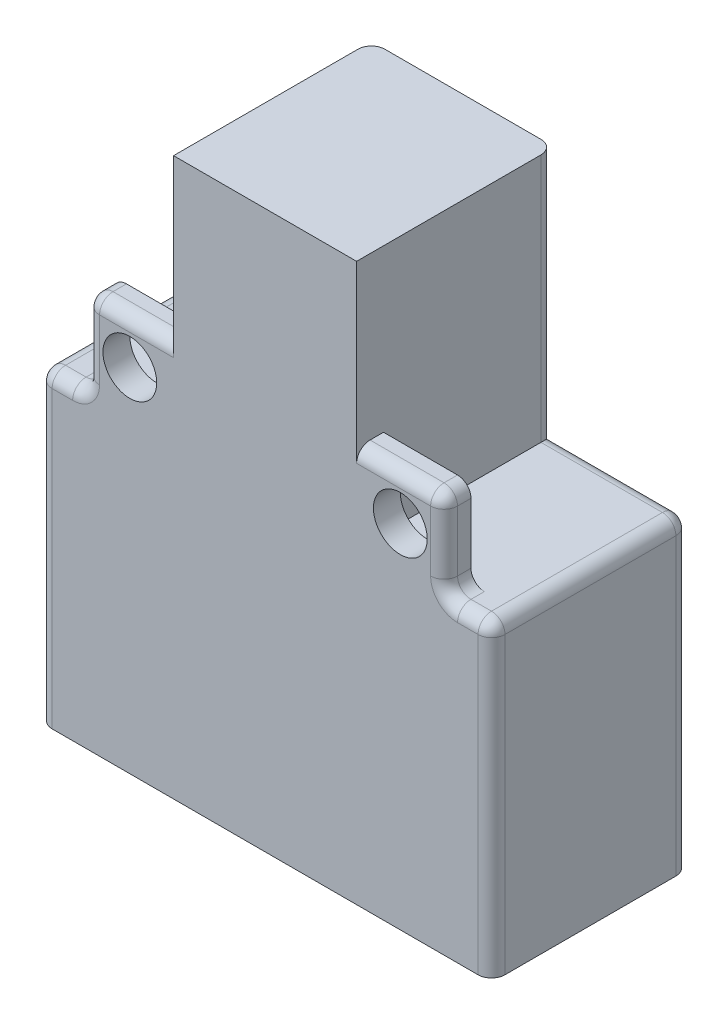
SolidWorks part; units mm, degrees
material "Custom Plastic"
ref_plane "Front Plane" through (0, 0, 0) normal (0, 0, 1) x (1, 0, 0)
ref_plane "Top Plane" through (0, 0, 0) normal (0, 1, 0) x (1, 0, 0)
ref_plane "Right Plane" through (0, 0, 0) normal (1, 0, 0) x (0, 0, -1)
sketch "Sketch1" plane through (0, 0, 0) normal (0, 1, 0) x (1, 0, 0)
  line L1 (-10.3392, 6.7346) -> (23.3108, 6.7346)
  line L2 (-10.3392, 6.7346) -> (-10.3392, -7.9654)
  line L3 (-10.3392, -7.9654) -> (23.3108, -7.9654)
  line L4 (23.3108, 6.7346) -> (23.3108, -7.9654)
  dimension "D1" = 14.7
  dimension "D2" = 33.65
extrude "Boss-Extrude1" add sketch "Sketch1" along normal blind 22.9
sketch "Sketch2" plane through (0, 22.9, 0) normal (0, 1, 0) x (1, 0, 0)
  line L0 (23.3108, 6.7346) -> (-10.3392, 6.7346) construction
  line L1 (-0.3142, 6.7346) -> (13.2858, 6.7346)
  line L2 (-0.3142, 6.7346) -> (-0.3142, -7.9654)
  line L3 (-0.3142, -7.9654) -> (13.2858, -7.9654)
  line L4 (13.2858, 6.7346) -> (13.2858, -7.9654)
  line L5 (-10.3392, -7.9654) -> (23.3108, -7.9654) construction
  line L6 (23.3108, -7.9654) -> (23.3108, 6.7346) construction
  dimension "D1" = 10.025
  dimension "D2" = 10.025
extrude "Boss-Extrude2" add sketch "Sketch2" along normal blind 18.5
sketch "Sketch3" plane through (0, 22.9, 0) normal (0, 1, 0) x (1, 0, 0)
  line L0 (-0.3142, 6.7346) -> (-0.3142, -7.9654) construction
  line L1 (-0.3142, -5.9654) -> (-6.8142, -5.9654)
  line L2 (-0.3142, -5.9654) -> (-0.3142, -7.9654)
  line L3 (-0.3142, -7.9654) -> (-6.8142, -7.9654)
  line L4 (-6.8142, -5.9654) -> (-6.8142, -7.9654)
  line L5 (-10.3392, -7.9654) -> (-0.3142, -7.9654) construction
  dimension "D1" = 6.5
  dimension "D2" = 2
extrude "Boss-Extrude3" add sketch "Sketch3" along normal blind 6.5
sketch "Sketch4" plane through (0, 22.9, 0) normal (0, 1, 0) x (1, 0, 0)
  line L0 (13.2858, -7.9654) -> (13.2858, 6.7346) construction
  line L1 (13.2858, -5.9654) -> (19.7858, -5.9654)
  line L2 (13.2858, -5.9654) -> (13.2858, -7.9654)
  line L3 (13.2858, -7.9654) -> (19.7858, -7.9654)
  line L4 (19.7858, -5.9654) -> (19.7858, -7.9654)
  line L5 (13.2858, -7.9654) -> (23.3108, -7.9654) construction
  dimension "D1" = 6.5
  dimension "D2" = 2
extrude "Boss-Extrude4" add sketch "Sketch4" along normal blind 6.5
sketch "Sketch5" plane through (0, 0, 5.9654) normal (0, 0, -1) x (-1, 0, 0)
  line L0 (3.5642, 29.4) -> (3.5642, 22.9) construction
  line L1 (0.3142, 29.4) -> (6.8142, 29.4) construction
  line L2 (0.3142, 22.9) -> (6.8142, 22.9) construction
  line L3 (0.3142, 26.15) -> (6.8142, 26.15) construction
  line L4 (0.3142, 29.4) -> (0.3142, 22.9) construction
  line L5 (6.8142, 29.4) -> (6.8142, 22.9) construction
  circle A0 centre (3.5642, 26.15) radius 1.9965
extrude "Cut-Extrude1" cut sketch "Sketch5" against normal mid plane 7.5 contours A0
sketch "Sketch6" plane through (0, 0, 5.9654) normal (0, 0, -1) x (-1, 0, 0)
  line L0 (-16.5358, 29.4) -> (-16.5358, 22.9) construction
  line L1 (-19.7858, 29.4) -> (-13.2858, 29.4) construction
  line L2 (-19.7858, 22.9) -> (-13.2858, 22.9) construction
  line L3 (-19.7858, 26.15) -> (-13.2858, 26.15) construction
  line L4 (-19.7858, 29.4) -> (-19.7858, 22.9) construction
  line L5 (-13.2858, 29.4) -> (-13.2858, 22.9) construction
  circle A0 centre (-16.5358, 26.15) radius 2
  dimension "D1" = 4
extrude "Cut-Extrude2" cut sketch "Sketch6" against normal mid plane 7.5
fillet "Fillet2" radius 1 6 edges at (19.7858, 22.9, 6.9654) (-6.8142, 22.9, 6.9654) (19.7858, 29.4, 6.9654) (-6.8142, 29.4, 6.9654) (-10.3392, 22.9, 0.6154) (23.3108, 22.9, 0.6154)
fillet "Fillet3" radius 1 22 edges at (16.0358, 29.4, 7.9654) (19.4929, 29.1071, 7.9654) (19.7858, 26.15, 7.9654) (20.0787, 23.1929, 7.9654) (21.5483, 22.9, 7.9654) (23.0179, 22.6071, 7.9654) (-3.0642, 29.4, 7.9654) (-6.5213, 29.1071, 7.9654) (-6.8142, 26.15, 7.9654) (-7.1071, 23.1929, 7.9654) (-8.5767, 22.9, 7.9654) (-10.0463, 22.6071, 7.9654) (23.0179, 22.6071, -6.7346) (-10.0463, 22.6071, -6.7346) (23.3108, 10.95, 7.9654) (-10.3392, 10.95, 7.9654) (-10.3392, 10.95, -6.7346) (23.3108, 10.95, -6.7346) (17.7983, 22.9, -6.7346) (-4.8267, 22.9, -6.7346) (-0.3142, 32.15, -6.7346) (13.2858, 32.15, -6.7346)
